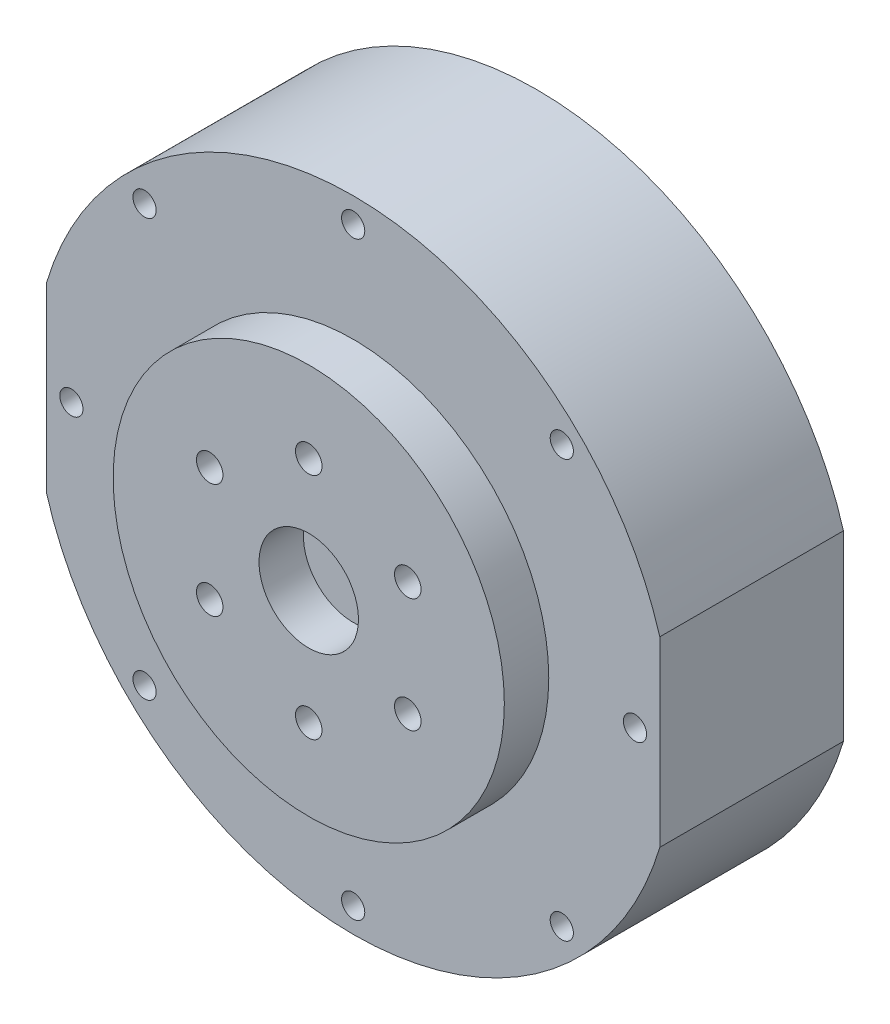
SolidWorks part; units mm, degrees
material "6063-O，挤压棒材(SS)"
ref_plane "前视基准面" through (0, 0, 0) normal (0, 0, 1) x (1, 0, 0)
ref_plane "上视基准面" through (0, 0, 0) normal (0, 1, 0) x (1, 0, 0)
ref_plane "右视基准面" through (0, 0, 0) normal (1, 0, 0) x (0, 0, -1)
other "Configuration Table"
sketch "草图1" plane through (0, 0, 0) normal (0, 0, 1) x (1, 0, 0)
  circle A0 centre (0, 0) radius 48.25
  dimension "D1" = 96.5
extrude "凸台-拉伸1" add sketch "草图1" along normal blind 27.7
sketch "草图2" plane through (0, 0, 0) normal (0, 0, -1) x (-1, 0, 0)
  circle A0 centre (0, 0) radius 29
  dimension "D1" = 58
extrude "凸台-拉伸2" add sketch "草图2" along normal blind 8
sketch "草图3" plane through (0, 0, 27.7) normal (0, 0, 1) x (1, 0, 0)
  circle A0 centre (0, 0) radius 29.5
  circle A1 centre (0, 0) radius 17.25 construction
  circle A2 centre (0, 17.25) radius 2
  circle A3 centre (14.9389, 8.625) radius 2
  circle A4 centre (14.9389, -8.625) radius 2
  circle A5 centre (0, -17.25) radius 2
  circle A6 centre (-14.9389, -8.625) radius 2
  circle A7 centre (-14.9389, 8.625) radius 2
  circle A8 centre (0, 0) radius 7.5
  point P18 (0, 0)
  dimension "D1" = 59
  dimension "D2" = 34.5
  dimension "D3" = 4
  dimension "D5" = 15
  dimension "D4" = 6
extrude "凸台-拉伸3" add sketch "草图3" along normal blind 6.7
sketch "草图4" plane through (0, 0, 27.7) normal (0, 0, 1) x (1, 0, 0)
  line L0 (-44.5, 0) -> (44.5, 0) construction
  line L1 (0, 44.5) -> (0, -44.5) construction
  circle A0 centre (0, 0) radius 44.5 construction
  circle A1 centre (0, 44.5) radius 1.75
  circle A2 centre (31.4663, 31.4663) radius 1.75
  circle A3 centre (44.5, 0) radius 1.75 construction
  circle A4 centre (31.4663, -31.4663) radius 1.75
  circle A5 centre (0, -44.5) radius 1.75
  circle A6 centre (-31.4663, -31.4663) radius 1.75
  circle A7 centre (-44.5, 0) radius 1.75 construction
  circle A8 centre (-31.4663, 31.4663) radius 1.75
  circle A9 centre (-42.5, 0) radius 1.75
  circle A10 centre (42.5, 0) radius 1.75
  point P21 (0, 0)
  dimension "D1" = 89
  dimension "D2" = 3.5
  dimension "D4" = 3.5
  dimension "D5" = 85
  dimension "D3" = 8
extrude "切除-拉伸1" cut sketch "草图4" against normal blind 5
sketch "草图5" plane through (0, 0, 0) normal (0, 0, -1) x (-1, 0, 0)
  circle A0 centre (0, 0) radius 42.5 construction
  circle A1 centre (0, 42.5) radius 1.75
  circle A2 centre (30.052, 30.052) radius 1.75
  circle A3 centre (42.5, 0) radius 1.75
  circle A4 centre (30.052, -30.052) radius 1.75
  circle A5 centre (0, -42.5) radius 1.75
  circle A6 centre (-30.052, -30.052) radius 1.75
  circle A7 centre (-42.5, 0) radius 1.75
  circle A8 centre (-30.052, 30.052) radius 1.75
  point P21 (0, 0)
  dimension "D1" = 3.5
  dimension "D3" = 85
  dimension "D2" = 8
extrude "切除-拉伸2" cut sketch "草图5" against normal blind 5
sketch "草图6" plane through (0, 0, 27.7) normal (0, 0, 1) x (1, 0, 0)
  line L0 (-46.25, 13.7477) -> (-46.25, -13.7477)
  line L1 (46.25, -13.7477) -> (46.25, 13.7477)
  line L2 (0, 48.25) -> (0, -48.25) construction
  arc A0 (-46.25, 13.7477) -> (-46.25, -13.7477) centre (0, 0) ccw
  arc A1 (46.25, -13.7477) -> (46.25, 13.7477) centre (0, 0) ccw
  dimension "D1" = 96.5
  dimension "D2" = 92.5
extrude "切除-拉伸3" cut sketch "草图6" against normal through all
ref_plane "基准面1" through (0, 0, 0) normal (0, 1, 0) x (1, 0, 0)
ref_plane "基准面2" through (0, 0, 0) normal (-1, 0, 0) x (0, 0, 1)
